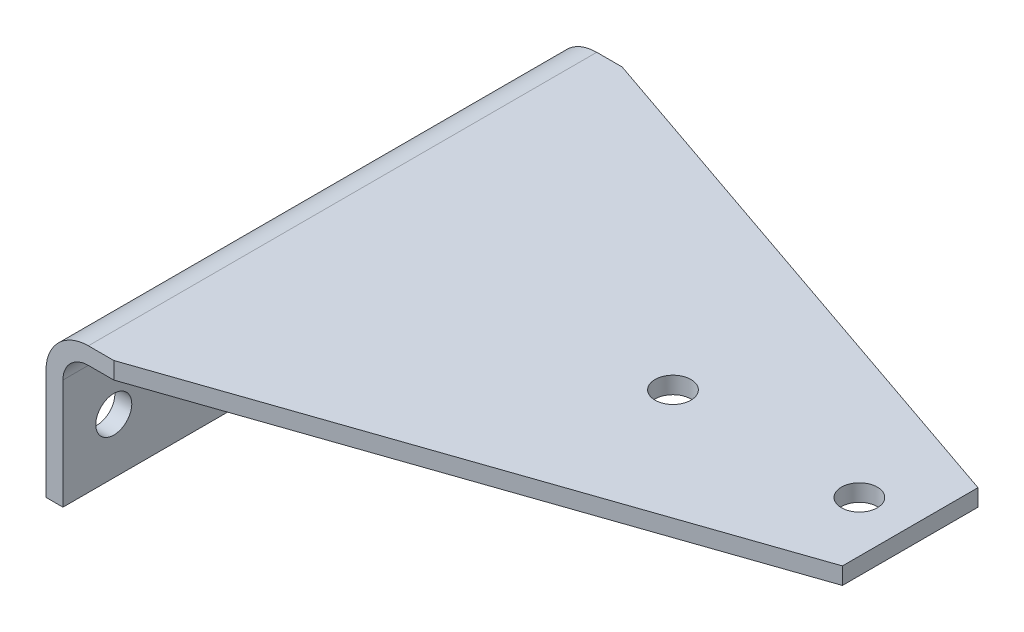
SolidWorks part; units mm, degrees
material "ASTM A36"
ref_plane "Front" through (0, 0, 0) normal (0, 0, 1) x (1, 0, 0)
ref_plane "Top" through (0, 0, 0) normal (0, 1, 0) x (1, 0, 0)
ref_plane "Side" through (0, 0, 0) normal (1, 0, 0) x (0, 0, -1)
sketch "Sketch1" plane through (0, 0, 0) normal (0, 0, 1) x (1, 0, 0)
  line L0 (228.6, 0) -> (15.875, 0)
  line L1 (0, -15.875) -> (0, -57.15)
  line L2 (0, -57.15) -> (6.35, -57.15)
  line L3 (6.35, -57.15) -> (6.35, -15.875)
  line L4 (15.875, -6.35) -> (228.6, -6.35)
  line L5 (228.6, -6.35) -> (228.6, 0)
  line L6 (50, 0) -> (-50, 0) construction
  arc A0 (15.875, 0) -> (0, -15.875) centre (15.875, -15.875) ccw
  arc A1 (6.35, -15.875) -> (15.875, -6.35) centre (15.875, -15.875) cw
  dimension "D3" = 9.525
  dimension "D1" = 228.6
  dimension "D2" = 57.15
  dimension "D4" = 6.35
extrude "Extrude1" add sketch "Sketch1" against normal mid plane 190.5
sketch "Sketch2" plane through (0, 0, 0) normal (0, 1, 0) x (1, 0, 0)
  line L0 (25.4, 95.25) -> (228.6, 25.4)
  line L1 (228.6, 95.25) -> (15.875, 95.25) construction
  line L2 (228.6, 95.25) -> (228.6, -95.25) construction
  line L3 (0, -50) -> (0, 50) construction
  line L4 (-50, 0) -> (50, 0) construction
  line L5 (0, 0) -> (258.8616, 0) construction
  line L6 (228.6, 25.4) -> (228.6, 95.25)
  line L7 (228.6, 95.25) -> (25.4, 95.25)
  line L8 (25.4, -95.25) -> (228.6, -25.4)
  line L9 (228.6, -95.25) -> (25.4, -95.25)
  line L10 (228.6, -25.4) -> (228.6, -95.25)
  line L11 (0, 0) -> (139.7, 0) construction
  line L12 (139.7, 0) -> (209.55, 0) construction
  circle A2 centre (209.55, 0) radius 6.731
  circle A3 centre (139.7, 0) radius 6.731
  dimension "D5" = 69.85
  dimension "D6" = 13.462
  dimension "D1" = 25.4
  dimension "D2" = 25.4
  dimension "D3" = 25.4
  dimension "D4" = 139.7
extrude "Cut-Chamfer" cut sketch "Sketch2" along normal blind 508 and the other way through all
sketch "Sketch3" plane through (0, 0, 0) normal (1, 0, 0) x (0, 0, -1)
  line L0 (50, 0) -> (-50, 0) construction
  line L1 (0, 0) -> (0, -94.016) construction
  circle A0 centre (-76.2, -36.5125) radius 6.7469
  circle A1 centre (76.2, -36.5125) radius 6.7469
  dimension "D2" = 152.4
  dimension "D3" = 13.4937
  dimension "D1" = 36.5125
extrude "Cut-Holes" cut sketch "Sketch3" along normal through all
